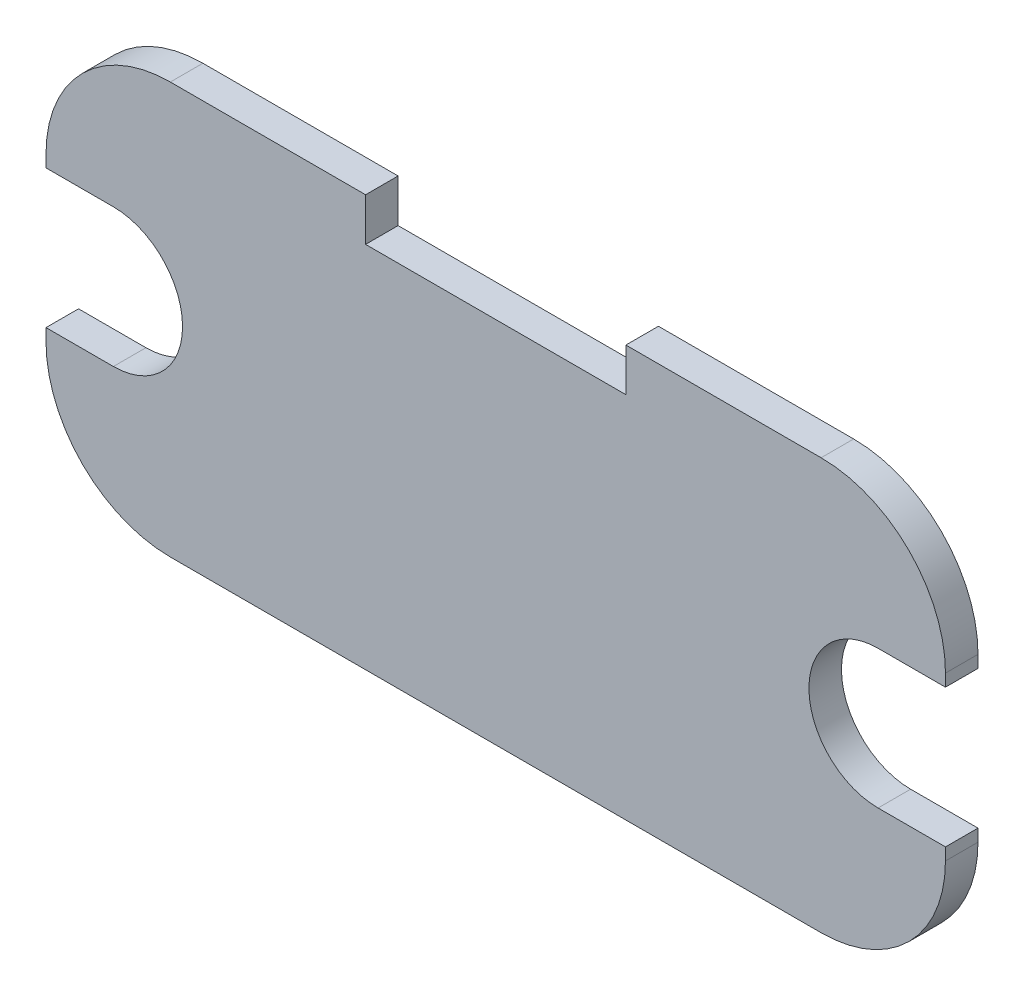
SolidWorks part; units mm, degrees
ref_plane "Спереди" through (0, 0, 0) normal (0, 0, 1) x (1, 0, 0)
ref_plane "Сверху" through (0, 0, 0) normal (0, 1, 0) x (1, 0, 0)
ref_plane "Справа" through (0, 0, 0) normal (1, 0, 0) x (0, 0, -1)
sketch "Эскиз1" plane through (0, 0, 0) normal (0, 0, 1) x (1, 0, 0)
  line L0 (-28.5, 3) -> (28.5, 3) construction
  line L1 (-20, 16.5) -> (-20, -10.5) construction
  line L2 (0, 16.5) -> (0, -10.5) construction
  line L3 (-20, 15.6424) -> (20, 15.6424)
  line L4 (-20, -9.6424) -> (20, -9.6424)
  line L5 (-27.6424, 8) -> (-27.6424, -2)
  line L6 (27.6424, 8) -> (27.6424, -2)
  line L7 (-8, 15.6424) -> (-8, 13)
  line L8 (28.5, 8) -> (28.5, -2)
  line L9 (-20, -10.5) -> (20, -10.5)
  line L10 (-28.5, 8) -> (-28.5, -2)
  line L11 (-8, 15) -> (-8, 13)
  line L12 (-8, 13) -> (8, 13)
  line L13 (8, 13) -> (8, 15)
  line L14 (8, 15) -> (-8, 15)
  line L15 (-20, 16.5) -> (20, 16.5)
  line L16 (8, 13) -> (8, 15.6424)
  circle A0 centre (-20, 8) radius 7.6424
  circle A1 centre (-20, -2) radius 7.6424
  circle A2 centre (20, -2) radius 7.6424
  circle A3 centre (20, 8) radius 7.6424
  arc A6 (20, -10.5) -> (28.5, -2) centre (20, -2) ccw
  arc A7 (-28.5, -2) -> (-20, -10.5) centre (-20, -2) ccw
  circle A8 centre (-23.5, 3) radius 3.25
  arc A10 (28.5, 8) -> (20, 16.5) centre (20, 8) ccw
  arc A11 (-20, 16.5) -> (-28.5, 8) centre (-20, 8) ccw
  circle A15 centre (23.5, 3) radius 3.25
extrude "Бобышка-Вытянуть1" add sketch "Эскиз1" along normal blind 2 contours A2 A3 L3 L16 L13 L12 L7 A0 A1 L4 | A8 A1 A0 | A8 A0 A1 | A8 A1 A0 | A8 A0 L5 A1 | A15 A3 A2 | A15 A3 A2 | A15 A2 A3 | A15 A2 L6 A3
sketch "Эскиз3" plane through (0, 0, 2) normal (0, 0, 1) x (1, 0, 0)
  line L0 (-23.5, 3) -> (-30.3035, 3) construction
  line L1 (-23.5, -1.25) -> (-30.3035, -1.25)
  line L2 (-23.5, 7.25) -> (-30.3035, 7.25)
  line L3 (0, 13) -> (0, -9.6424) construction
  line L4 (-8, 13) -> (8, 13) construction
  line L5 (-20, -9.6424) -> (20, -9.6424) construction
  line L6 (23.5, 3) -> (30.3035, 3) construction
  line L7 (23.5, -1.25) -> (30.3035, -1.25)
  line L8 (23.5, 7.25) -> (30.3035, 7.25)
  arc A0 (-23.5, -1.25) -> (-23.5, 7.25) centre (-23.5, 3) ccw
  arc A1 (-30.3035, 7.25) -> (-30.3035, -1.25) centre (-30.3035, 3) ccw
  circle A2 centre (-23.5, 3) radius 3.25 construction
  arc A3 (23.5, -1.25) -> (23.5, 7.25) centre (23.5, 3) cw
  arc A4 (30.3035, 7.25) -> (30.3035, -1.25) centre (30.3035, 3) cw
  point P3 (-26.9017, 3)
  point P18 (26.9017, 3)
  dimension "D1" = 1
extrude "Вырез-Вытянуть2" cut sketch "Эскиз3" against normal blind 2
sketch "Эскиз4" plane through (0, 0, 0) normal (0, 0, -1) x (-1, 0, 0)
  line L0 (-27.6424, 8) -> (-27.6424, 7.25) construction
  line L1 (-27.6424, 7.25) -> (-23.5, 7.25) construction
  line L2 (-27.6424, -1.25) -> (-27.6424, -2) construction
  line L3 (20, -9.6424) -> (-20, -9.6424) construction
  line L4 (-23.5, -1.25) -> (-27.6424, -1.25) construction
  line L5 (-8, 15.6424) -> (-20, 15.6424) construction
  line L6 (-8, 13) -> (-8, 15.6424) construction
  line L7 (8, 13) -> (-8, 13) construction
  line L8 (8, 15.6424) -> (8, 13) construction
  line L9 (20, 15.6424) -> (8, 15.6424) construction
  line L10 (27.6424, -1.25) -> (27.6424, -2) construction
  line L11 (27.6424, 8) -> (27.6424, 7.25) construction
  line L12 (23.5, 7.25) -> (27.6424, 7.25) construction
  line L13 (27.6424, -1.25) -> (23.5, -1.25) construction
  line L14 (-27.6424, 8) -> (-27.6424, 7.25)
  line L15 (-27.6424, -1.25) -> (-27.6424, -2)
  line L16 (20, -9.6424) -> (-20, -9.6424)
  line L17 (-23.5, -1.25) -> (-27.6424, -1.25)
  line L18 (-27.6424, 7.25) -> (-23.5, 7.25)
  line L19 (-8, 15.6424) -> (-20, 15.6424)
  line L20 (-8, 13) -> (-8, 15.6424)
  line L21 (8, 13) -> (-8, 13)
  line L22 (8, 15.6424) -> (8, 13)
  line L23 (20, 15.6424) -> (8, 15.6424)
  line L24 (27.6424, -1.25) -> (27.6424, -2)
  line L25 (27.6424, 8) -> (27.6424, 7.25)
  line L26 (23.5, 7.25) -> (27.6424, 7.25)
  line L27 (27.6424, -1.25) -> (23.5, -1.25)
  arc A0 (-20, 15.6424) -> (-27.6424, 8) centre (-20, 8) ccw construction
  arc A1 (-27.6424, -2) -> (-20, -9.6424) centre (-20, -2) ccw construction
  arc A2 (-23.5, -1.25) -> (-23.5, 7.25) centre (-23.5, 3) ccw construction
  arc A3 (27.6424, 8) -> (20, 15.6424) centre (20, 8) ccw construction
  arc A4 (23.5, 7.25) -> (23.5, -1.25) centre (23.5, 3) ccw construction
  arc A5 (20, -9.6424) -> (27.6424, -2) centre (20, -2) ccw construction
  arc A6 (-27.6424, -2) -> (-20, -9.6424) centre (-20, -2) ccw
  arc A7 (-23.5, -1.25) -> (-23.5, 7.25) centre (-23.5, 3) ccw
  arc A8 (-20, 15.6424) -> (-27.6424, 8) centre (-20, 8) ccw
  arc A9 (27.6424, 8) -> (20, 15.6424) centre (20, 8) ccw
  arc A10 (23.5, 7.25) -> (23.5, -1.25) centre (23.5, 3) ccw
  arc A11 (20, -9.6424) -> (27.6424, -2) centre (20, -2) ccw
